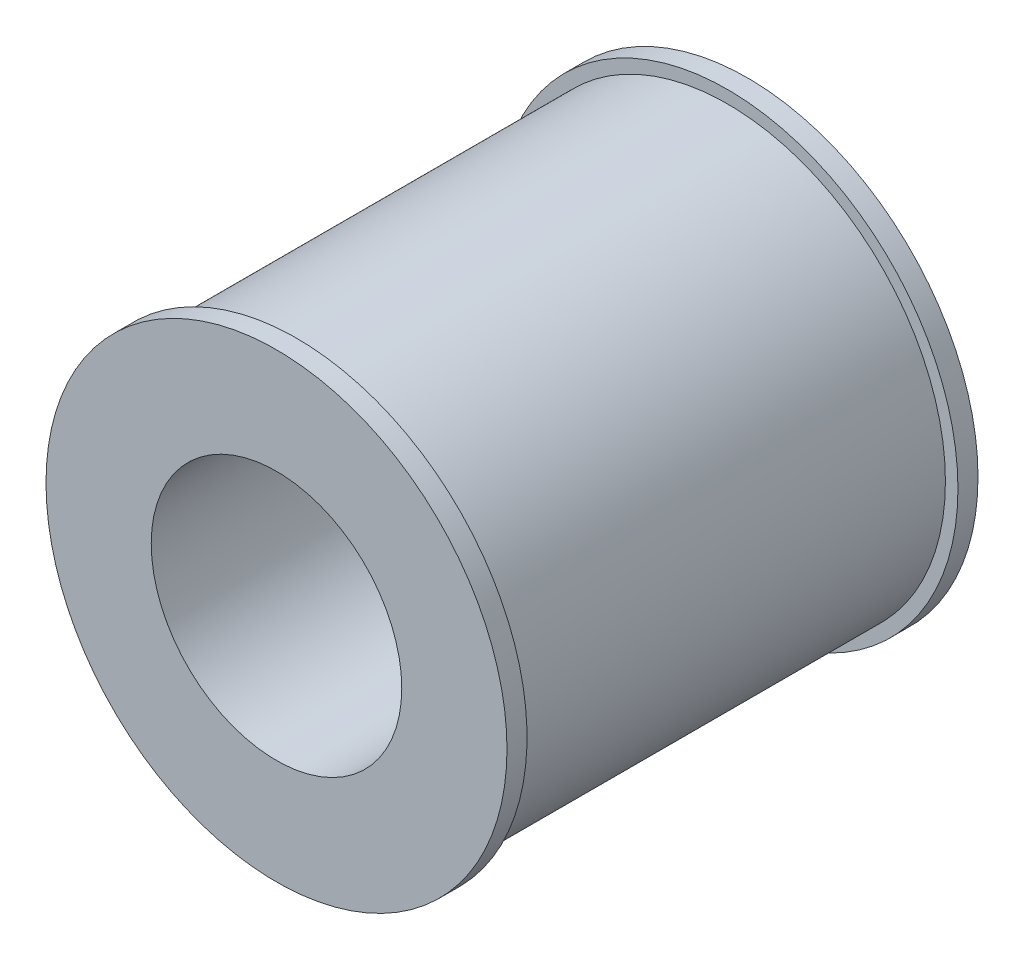
SolidWorks part; units mm, degrees
material "Резина"
ref_plane "Спереди" through (0, 0, 0) normal (0, 0, 1) x (1, 0, 0)
ref_plane "Сверху" through (0, 0, 0) normal (0, 1, 0) x (1, 0, 0)
ref_plane "Справа" through (0, 0, 0) normal (1, 0, 0) x (0, 0, -1)
sketch "Эскиз1" plane through (0, 0, 0) normal (0, 0, 1) x (1, 0, 0)
  circle A0 centre (0, 0) radius 23
  circle A1 centre (0, 0) radius 12.5
  dimension "D1" = 46
  dimension "D2" = 25
extrude "Бобышка-Вытянуть1" add sketch "Эскиз1" along normal blind 47
sketch "Эскиз2" plane through (0, 0, 0) normal (1, 0, 0) x (0, 0, -1)
  line L0 (-47, 0) -> (0, 0) construction
  line L1 (-47, 23) -> (-47, -23) construction
  line L2 (-23.5, 0) -> (-23.5, 23) construction
  line L3 (0, 23) -> (-47, 23) construction
  line L5 (-45, 21.75) -> (-2, 21.75)
  line L6 (-45, 21.75) -> (-45, 24.25)
  line L7 (-45, 24.25) -> (-2, 24.25)
  line L8 (-2, 21.75) -> (-2, 24.25)
  line L9 (-45, 21.75) -> (-2, 24.25) construction
  line L10 (-45, 24.25) -> (-2, 21.75) construction
  dimension "D1" = 2.5
  dimension "D2" = 2
revolve "Вырез-Повернуть1" cut sketch "Эскиз2" angle 360 about L0
